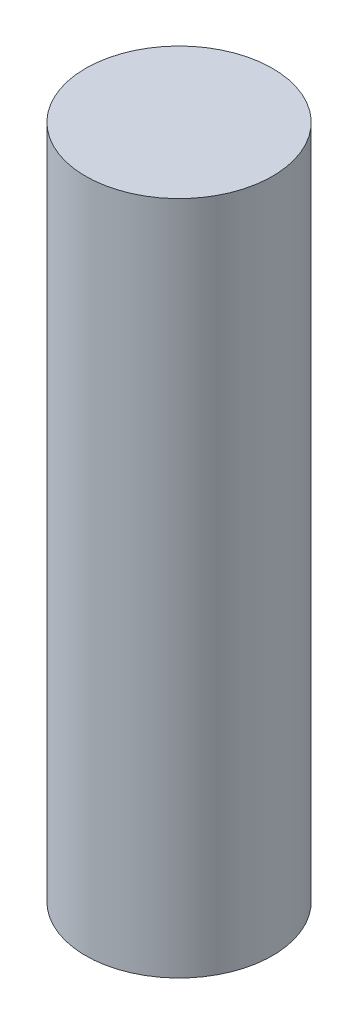
SolidWorks part; units mm, degrees
ref_plane "Plano frontal" through (0, 0, 0) normal (0, 0, 1) x (1, 0, 0)
ref_plane "Plano superior" through (0, 0, 0) normal (0, 1, 0) x (1, 0, 0)
ref_plane "Plano direito" through (0, 0, 0) normal (1, 0, 0) x (0, 0, -1)
sketch "Esboço1" plane through (0, 0, 0) normal (0, 0, 1) x (1, 0, 0)
  line L0 (0, 0) -> (9, 0)
  line L1 (9, 0) -> (9, 65)
  line L2 (9, 65) -> (0, 65)
  line L3 (0, 65) -> (0, 0) construction
  line L4 (0, 0) -> (0, 65)
  dimension "D1" = 18
  dimension "D2" = 65
revolve "Revolução1" add sketch "Esboço1" angle 360 about L3
